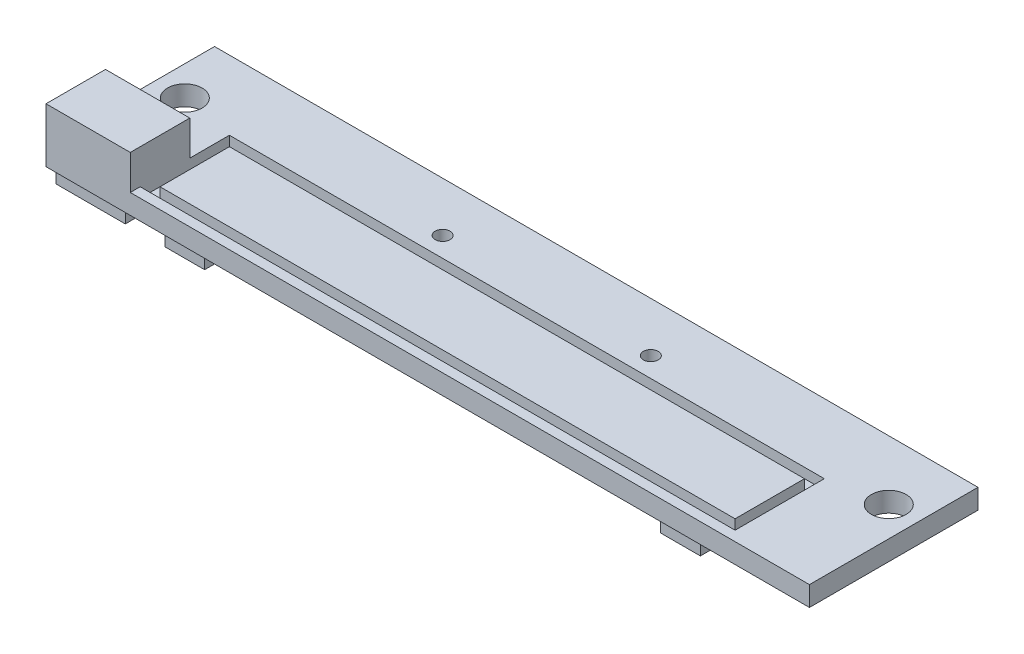
SolidWorks part; units mm, degrees
ref_plane "Plan de face" through (0, 0, 0) normal (0, 0, 1) x (1, 0, 0)
ref_plane "Plan de dessus" through (0, 0, 0) normal (0, 1, 0) x (1, 0, 0)
ref_plane "Plan de droite" through (0, 0, 0) normal (1, 0, 0) x (0, 0, -1)
sketch "Esquisse1" plane through (0, 0, 0) normal (0, 1, 0) x (1, 0, 0)
  line L1 (0, 0) -> (77, 0)
  line L2 (0, 0) -> (0, 17)
  line L3 (0, 17) -> (77, 17)
  line L4 (77, 0) -> (77, 17)
  dimension "D1" = 77
  dimension "D2" = 17
extrude "Boss.-Extru.1" add sketch "Esquisse1" along normal blind 2
sketch "Esquisse2" plane through (0, 2, 0) normal (0, 1, 0) x (1, 0, 0)
  line L0 (0, 0) -> (77, 0) construction
  line L1 (8.5, 10) -> (68.5, 10)
  line L2 (8.5, 10) -> (8.5, 1)
  line L3 (8.5, 1) -> (68.5, 1)
  line L4 (68.5, 10) -> (68.5, 1)
  line L5 (38.5, 0) -> (38.5, 1) construction
  line L6 (9.5, 9) -> (9.5, 2)
  line L7 (9.5, 2) -> (67.5, 2)
  line L12 (67.5, 9) -> (67.5, 2)
  line L13 (9.5, 9) -> (67.5, 9)
  point P10 (38.5, 1)
  dimension "D1" = 60
  dimension "D2" = 9
  dimension "D3" = 1
  dimension "D4" = 1
extrude "Enlèv. mat.-Extru.1" cut sketch "Esquisse2" against normal blind 1
sketch "Esquisse3" plane through (0, 2, 0) normal (0, 1, 0) x (1, 0, 0)
  line L0 (8.5, 10) -> (8.5, 1) construction
  line L1 (0, 0) -> (8.5, 0)
  line L2 (0, 0) -> (0, 6)
  line L3 (0, 6) -> (8.5, 6)
  line L4 (8.5, 0) -> (8.5, 6)
  dimension "D1" = 6
extrude "Boss.-Extru.2" add sketch "Esquisse3" along normal blind 3.5
sketch "Esquisse4" plane through (0, 2, 0) normal (0, 1, 0) x (1, 0, 0)
  line L0 (77, 0) -> (77, 17) construction
  line L1 (77, 17) -> (0, 17) construction
  line L2 (38.5, 17) -> (38.5, 0) construction
  line L3 (8.5, 0) -> (77, 0) construction
  circle A0 centre (74, 11) radius 1.75
  circle A1 centre (49, 12) radius 0.75
  circle A2 centre (3, 11) radius 1.75
  circle A3 centre (28, 12) radius 0.75
  dimension "D1" = 3.5
  dimension "D2" = 3
  dimension "D4" = 1.5
  dimension "D5" = 28
  dimension "D6" = 5
  dimension "D3" = 6
extrude "Enlèv. mat.-Extru.2" cut sketch "Esquisse4" against normal through all
sketch "Esquisse5" plane through (0, 0, 0) normal (0, -1, 0) x (1, 0, 0)
  line L0 (0, 0) -> (77, 0) construction
  line L1 (0.5, -0.5) -> (7.5, -0.5)
  line L2 (0.5, -0.5) -> (0.5, -3)
  line L3 (0.5, -3) -> (7.5, -3)
  line L4 (7.5, -0.5) -> (7.5, -3)
  line L5 (0, -17) -> (0, 0) construction
  line L6 (38.5, -17) -> (38.5, 0) construction
  line L7 (7, -3.1) -> (9.5, -3.1)
  line L8 (7, -3.1) -> (7, -8.6)
  line L9 (7, -8.6) -> (9.5, -8.6)
  line L10 (9.5, -3.1) -> (9.5, -8.6)
  line L11 (13, -9) -> (17, -9)
  line L12 (13, -9) -> (13, -12)
  line L13 (13, -12) -> (17, -12)
  line L14 (17, -9) -> (17, -12)
  line L15 (11.5, -0.5) -> (15.5, -0.5)
  line L16 (11.5, -0.5) -> (11.5, -3.5)
  line L17 (11.5, -3.5) -> (15.5, -3.5)
  line L18 (15.5, -0.5) -> (15.5, -3.5)
  line L19 (77, -17) -> (0, -17) construction
  line L20 (70, -8.6) -> (67.5, -8.6)
  line L21 (67.5, -3.1) -> (67.5, -8.6)
  line L22 (70, -3.1) -> (67.5, -3.1)
  line L23 (70, -3.1) -> (70, -8.6)
  line L24 (60, -9) -> (60, -12)
  line L25 (64, -12) -> (60, -12)
  line L26 (64, -9) -> (64, -12)
  line L27 (64, -9) -> (60, -9)
  line L28 (61.5, -0.5) -> (61.5, -3.5)
  line L29 (65.5, -0.5) -> (61.5, -0.5)
  line L30 (65.5, -0.5) -> (65.5, -3.5)
  line L31 (65.5, -3.5) -> (61.5, -3.5)
  point P16 (13, -10.5)
  dimension "D1" = 7
  dimension "D2" = 2.5
  dimension "D3" = 0.5
  dimension "D4" = 0.5
  dimension "D5" = 5.5
  dimension "D6" = 2.5
  dimension "D7" = 3.1
  dimension "D8" = 7
  dimension "D9" = 4
  dimension "D10" = 3
  dimension "D11" = 9
  dimension "D12" = 13
  dimension "D13" = 4
  dimension "D14" = 3
  dimension "D15" = 0.5
  dimension "D16" = 11.5
extrude "Boss.-Extru.3" add sketch "Esquisse5" along normal blind 1.5
